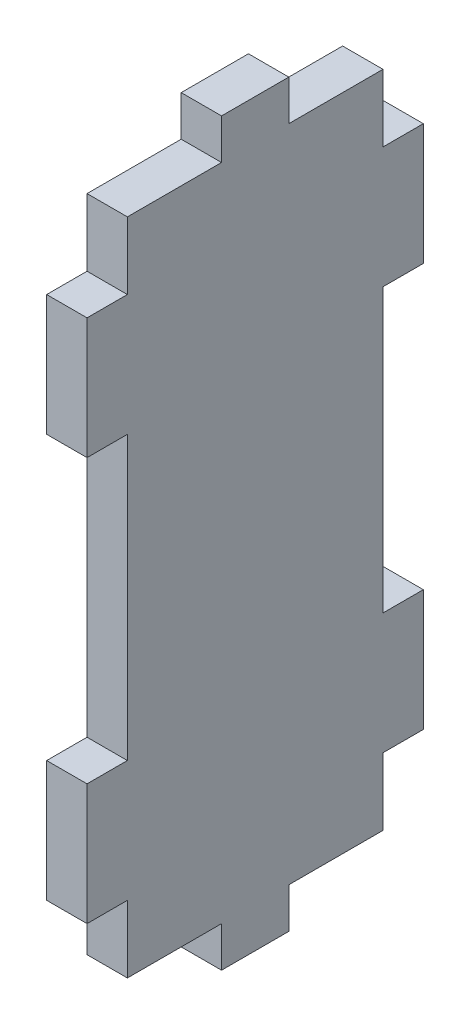
SolidWorks part; units mm, degrees
ref_plane "정면" through (0, 0, 0) normal (0, 0, 1) x (1, 0, 0)
ref_plane "윗면" through (0, 0, 0) normal (0, 1, 0) x (1, 0, 0)
ref_plane "우측면" through (0, 0, 0) normal (1, 0, 0) x (0, 0, -1)
sketch "스케치2" plane through (0, 0, 0) normal (1, 0, 0) x (0, 0, -1)
  line L1 (0, 0) -> (25, 0)
  line L2 (0, 0) -> (0, 55)
  line L3 (0, 55) -> (25, 55)
  line L4 (25, 0) -> (25, 55)
  dimension "D1" = 25
  dimension "D2" = 55
extrude "보스-돌출1" add sketch "스케치2" along normal blind 3
sketch "스케치3" plane through (3, 0, 0) normal (1, 0, 0) x (0, 0, -1)
  line L0 (0, 0) -> (25, 0) construction
  line L1 (0, 55) -> (3, 55)
  line L2 (0, 55) -> (0, 0)
  line L3 (0, 0) -> (3, 0)
  line L4 (3, 55) -> (3, 47)
  line L5 (3, 38) -> (3, 17)
  line L6 (0, 47) -> (3, 47)
  line L7 (0, 47) -> (0, 38)
  line L8 (0, 38) -> (3, 38)
  line L10 (0, 17) -> (3, 17)
  line L11 (0, 17) -> (0, 8)
  line L12 (0, 8) -> (3, 8)
  line L14 (3, 8) -> (3, 0)
  line L15 (12.5, 57.5115) -> (12.5, -1.9499) construction
  line L16 (25, 0) -> (22, 0)
  line L17 (22, 8) -> (22, 0)
  line L18 (25, 8) -> (22, 8)
  line L19 (25, 17) -> (22, 17)
  line L20 (22, 38) -> (22, 17)
  line L21 (25, 38) -> (22, 38)
  line L22 (25, 47) -> (22, 47)
  line L23 (25, 55) -> (22, 55)
  line L24 (25, 55) -> (25, 0)
  line L25 (22, 55) -> (22, 47)
  point P15 (1.5, 55)
  line M12 (0, 55) -> (0, 0)
  line M13 (0, 0) -> (25, 0)
  line M14 (25, 0) -> (25, 55)
  line M15 (25, 55) -> (0, 55)
  dimension "D1" = 3
  dimension "D2" = 8
  dimension "D3" = 9
  dimension "D4" = 8
  dimension "D5" = 9
extrude "컷-돌출1" cut sketch "스케치3" against normal through all contours L6 L4 M12 M15 | L25 L22 M15 M14 | L21 L20 L19 M14 | L10 L5 L8 M12 | L14 L12 M12 M13 | L18 L17 M14 M13
sketch "스케치4" plane through (3, 0, 0) normal (1, 0, 0) x (0, 0, -1)
  line L0 (22, 55) -> (22, 47) construction
  line L1 (3, 55) -> (22, 55)
  line L2 (3, 55) -> (3, 52)
  line L3 (3, 52) -> (10, 52)
  line L4 (22, 55) -> (22, 52)
  line L5 (15, 52) -> (22, 52)
  line L6 (10, 55) -> (15, 55)
  line L7 (10, 55) -> (10, 52)
  line L9 (15, 55) -> (15, 52)
  line L10 (-1.8915, 27.5) -> (27.8041, 27.5) construction
  line L11 (22, 0) -> (22, 3)
  line L12 (15, 3) -> (22, 3)
  line L13 (15, 0) -> (15, 3)
  line L14 (10, 0) -> (10, 3)
  line L15 (3, 3) -> (10, 3)
  line L16 (3, 0) -> (3, 3)
  line L17 (3, 0) -> (22, 0)
  point P11 (15, 53.5)
  line M9 (22, 47) -> (22, 55)
  line M10 (22, 55) -> (3, 55)
  line M11 (3, 55) -> (3, 47)
  line M19 (3, 8) -> (3, 0)
  line M20 (3, 0) -> (22, 0)
  line M21 (22, 0) -> (22, 8)
  dimension "D1" = 3
  dimension "D2" = 5
  dimension "D3" = 7
extrude "컷-돌출2" cut sketch "스케치4" against normal through all contours L7 L3 M10 M11 | L9 L5 M10 M9 | L13 L12 M20 M21 | L15 L14 M19 M20
